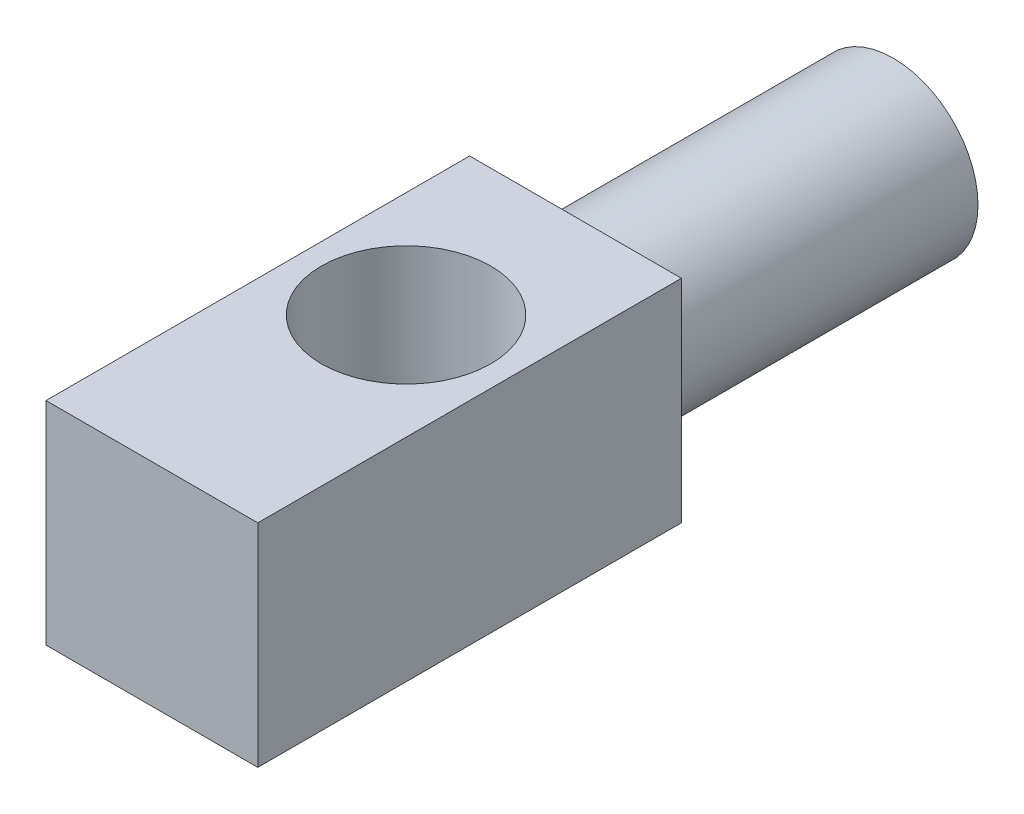
SolidWorks part; units mm, degrees
ref_plane "Alzado" through (0, 0, 0) normal (0, 0, 1) x (1, 0, 0)
ref_plane "Planta" through (0, 0, 0) normal (0, 1, 0) x (1, 0, 0)
ref_plane "Vista lateral" through (0, 0, 0) normal (1, 0, 0) x (0, 0, -1)
sketch "Croquis1" plane through (0, 0, 0) normal (0, 1, 0) x (1, 0, 0)
  line L0 (-25, 40) -> (-25, -60)
  line L1 (-25, -60) -> (25, -60)
  line L2 (25, -60) -> (25, 40)
  line L3 (25, 40) -> (-25, 40)
  circle A0 centre (0, 0) radius 20
  point P6 (0, 40)
  dimension "D1" = 40
  dimension "D2" = 40
  dimension "D3" = 60
  dimension "D4" = 50
extrude "Saliente-Extruir1" add sketch "Croquis1" along normal blind 50
sketch "Croquis2" plane through (0, 0, -40) normal (0, 0, -1) x (-1, 0, 0)
  circle A0 centre (0, 25) radius 20
  dimension "D1" = 40
extrude "Saliente-Extruir2" add sketch "Croquis2" along normal blind 75
